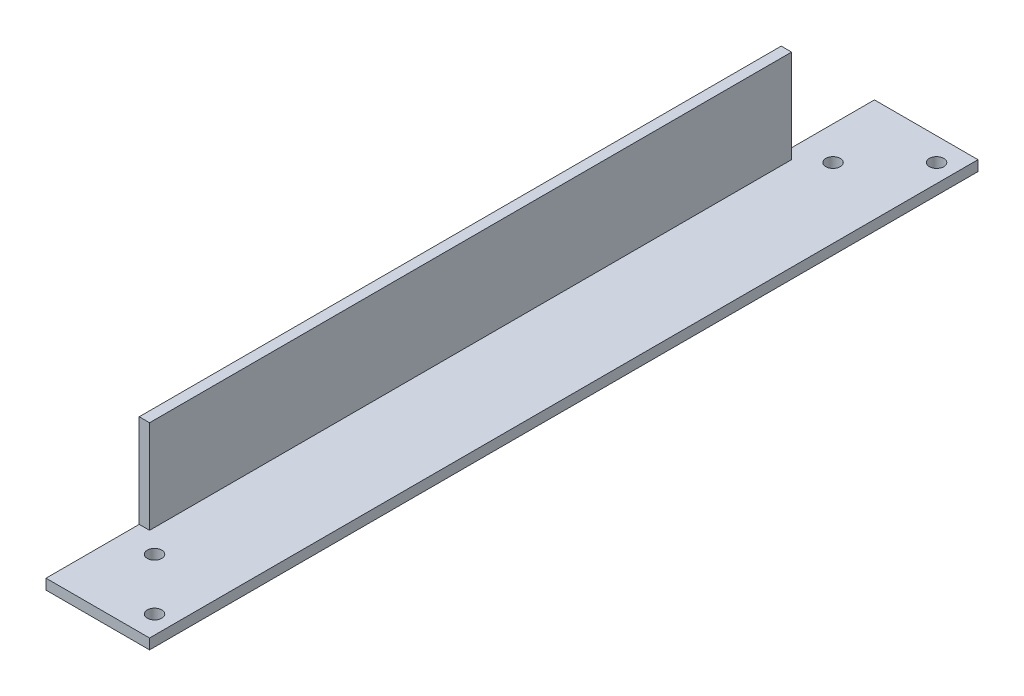
SolidWorks part; units mm, degrees
ref_plane "Plan de face" through (0, 0, 0) normal (0, 0, 1) x (1, 0, 0)
ref_plane "Plan de dessus" through (0, 0, 0) normal (0, 1, 0) x (1, 0, 0)
ref_plane "Plan de droite" through (0, 0, 0) normal (1, 0, 0) x (0, 0, -1)
sketch "Esquisse1" plane through (0, 0, 0) normal (0, 0, 1) x (1, 0, 0)
  line L0 (0, 0) -> (20, 0)
  line L1 (20, 0) -> (20, 2)
  line L2 (20, 2) -> (2, 2)
  line L3 (2, 2) -> (2, 20)
  line L4 (2, 20) -> (0, 20)
  line L5 (0, 20) -> (0, 0)
  dimension "D1" = 20
  dimension "D2" = 2
extrude "Boss.-Extru.1" add sketch "Esquisse1" along normal blind 160
sketch "Esquisse2" plane through (2, 0, 0) normal (1, 0, 0) x (0, 0, -1)
  line L0 (-160, 2) -> (0, 2) construction
  line L1 (-160, 20) -> (-142, 20)
  line L2 (-160, 20) -> (-160, 2)
  line L3 (-160, 2) -> (-142, 2)
  line L4 (-142, 20) -> (-142, 2)
  line L5 (-160, 2) -> (0, 2) construction
  line L6 (0, 20) -> (-18, 20)
  line L7 (0, 20) -> (0, 2)
  line L8 (0, 2) -> (-18, 2)
  line L9 (-18, 20) -> (-18, 2)
  dimension "D1" = 18
extrude "Enlèv. mat.-Extru.1" cut sketch "Esquisse2" against normal through all
sketch "Esquisse6" plane through (0, 2, 0) normal (0, 1, 0) x (1, 0, 0)
  line L0 (20, -80) -> (2, -80) construction
  line L1 (20, -160) -> (20, 0) construction
  line L2 (2, -142) -> (2, -18) construction
  line L3 (20, -160) -> (0, -160) construction
  line L4 (2, -142) -> (2, -18) construction
  line L5 (0, -160) -> (0, -142) construction
  circle A0 centre (6.48, -145.52) radius 1.4
  circle A1 centre (6.48, -14.48) radius 1.4
  circle A2 centre (16.48, -155.52) radius 1.4
  circle A3 centre (16.48, -4.48) radius 1.4
  dimension "D3" = 2.8
  dimension "D1" = 14.48
  dimension "D2" = 4.48
  dimension "D4" = 4.48
  dimension "D5" = 16.48
extrude "Enlèv. mat.-Extru.5" cut sketch "Esquisse6" against normal through all
